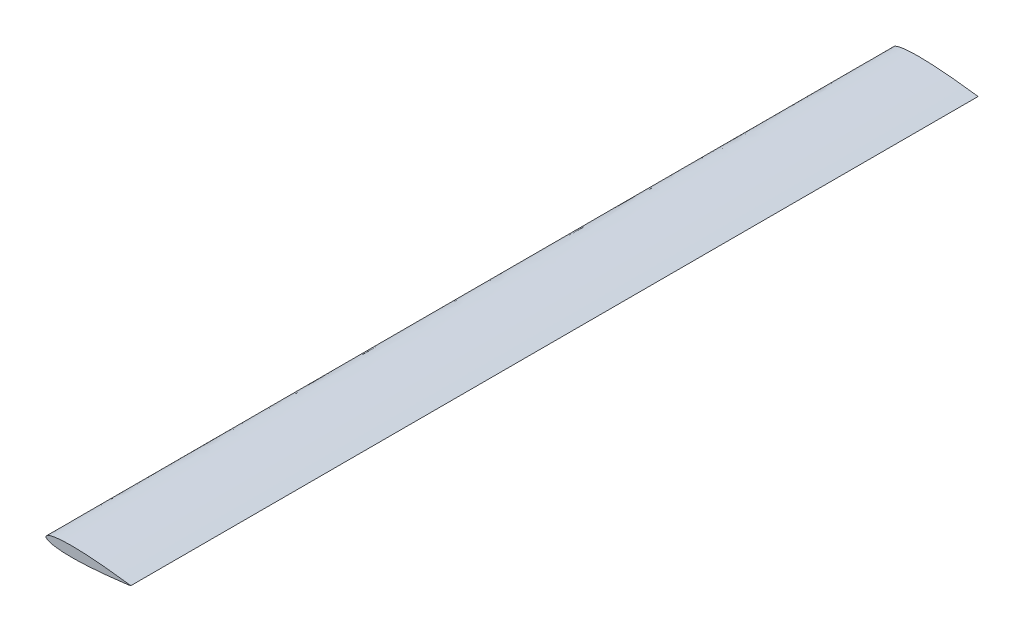
SolidWorks part; units mm, degrees
material "Custom Polymer"
ref_plane "Front Plane" through (0, 0, 0) normal (0, 0, 1) x (1, 0, 0)
ref_plane "Top Plane" through (0, 0, 0) normal (0, 1, 0) x (1, 0, 0)
ref_plane "Right Plane" through (0, 0, 0) normal (1, 0, 0) x (0, 0, -1)
other "Center of Mass"
sketch "Sketch1" plane through (0, 0, 0) normal (0, 0, 1) x (1, 0, 0)
  line L0 (0, 0) -> (1000, 0) construction
  spline S4 degree 3 poles (0.4143, 4.3853) (-0.2008, 0.0001) (0.4094, -4.3857) (2.2543, -8.6603) (5.2707, -12.775) (9.422, -16.7475) (14.6946, -20.592) (21.081, -24.312) (28.5717, -27.9033) (37.1535, -31.3578) (46.8093, -34.6651) (57.5186, -37.8143) (69.2578, -40.7934) (82.0003, -43.5917) (95.717, -46.1976) (110.3762, -48.6018) (125.9441, -50.7943) (142.3846, -52.7677) (159.6593, -54.5151) (177.7281, -56.0316) (196.5487, -57.3135) (216.0775, -58.3589) (236.2687, -59.1679) (257.0752, -59.7419) (278.4485, -60.0841) (300.3387, -60.1994) (322.6946, -60.0941) (345.4641, -59.7758) (368.5941, -59.2535) (392.0304, -58.5372) (415.7184, -57.6376) (439.6028, -56.5665) (463.6278, -55.336) (487.7372, -53.9588) (511.8749, -52.4476) (535.9844, -50.8155) (560.0094, -49.0752) (583.8939, -47.2399) (607.5819, -45.322) (631.0183, -43.3341) (654.1483, -41.2882) (676.9179, -39.1961) (699.2738, -37.0696) (721.1639, -34.9196) (742.5371, -32.7573) (763.3433, -30.5932) (783.5341, -28.438) (803.0622, -26.3022) (821.8821, -24.1954) (839.9497, -22.1283) (857.223, -20.1106) (873.6615, -18.1522) (889.2267, -16.2628) (903.8825, -14.4523) (917.5946, -12.7298) (930.3308, -11.1051) (942.0615, -9.5864) (952.7594, -8.1834) (962.3991, -6.9024) (970.9591, -5.7556) (978.4165, -4.737) (984.7625, -3.8911) (989.9579, -3.1155) (994.0559, -2.7031) (996.8878, -1.9572) (999.5116, -2.4521) (1000.4888, 0.7707) (998.6373, 0.7843) (996.9769, 1.1296) (994.0179, 1.481) (989.9767, 2.0732) (984.7604, 2.7864) (978.4232, 3.6639) (970.9642, 4.6823) (962.4063, 5.8413) (952.7678, 7.1321) (942.0716, 8.5471) (930.3425, 10.0787) (917.6081, 11.7175) (903.8979, 13.4551) (889.2441, 15.2818) (873.6809, 17.1884) (857.2446, 19.1649) (839.9736, 21.2016) (821.9083, 23.2886) (803.0908, 25.4162) (783.565, 27.5735) (763.3766, 29.751) (742.5728, 31.9381) (721.202, 34.124) (699.3143, 36.2981) (676.9607, 38.4492) (654.1935, 40.5664) (631.0658, 42.6379) (607.6316, 44.6517) (583.9456, 46.5957) (560.0632, 48.4573) (536.0401, 50.2241) (511.9324, 51.8829) (487.7965, 53.4207) (463.6885, 54.8245) (439.6649, 56.0815) (415.7818, 57.179) (392.0947, 58.1047) (368.6592, 58.8468) (345.5299, 59.3946) (322.7607, 59.7381) (300.4049, 59.868) (278.5146, 59.7768) (257.1409, 59.4583) (236.3338, 58.9072) (216.1417, 58.1205) (196.6118, 57.0967) (177.7898, 55.8354) (159.7194, 54.3389) (142.4427, 52.6106) (126.0001, 50.6553) (110.4297, 48.48) (95.7679, 46.092) (82.0483, 43.5012) (69.3028, 40.717) (57.5603, 37.7508) (46.8475, 34.6134) (37.188, 31.3167) (28.6024, 27.8718) (21.1078, 24.2887) (14.7173, 20.5758) (9.4405, 16.7371) (5.2848, 12.7691) (2.2639, 8.6578) (0.4143, 4.3853) (-0.2008, 0.0001) (0.4094, -4.3857) knots -0.006774 -0.004322 -0.002107 0 0.002107 0.004322 0.006774 0.009559 0.012737 0.016346 0.02041 0.02494 0.02994 0.03541 0.041346 0.047742 0.054587 0.061871 0.06958 0.077699 0.086213 0.095105 0.104356 0.113946 0.123856 0.134064 0.144547 0.155282 0.166246 0.177414 0.188761 0.20026 0.211886 0.223612 0.23541 0.247253 0.259115 0.270966 0.28278 0.294528 0.306184 0.31772 0.329108 0.340322 0.351336 0.362124 0.37266 0.382919 0.392878 0.402513 0.4118 0.42072 0.429249 0.437368 0.445058 0.452301 0.459079 0.465376 0.471177 0.476469 0.481238 0.485474 0.489166 0.492305 0.494884 0.496896 0.498337 0.499202 0.500509 0.500798 0.501663 0.503104 0.505116 0.507695 0.510834 0.514526 0.518762 0.523531 0.528823 0.534624 0.540921 0.547699 0.554942 0.562632 0.570751 0.57928 0.5882 0.597487 0.607122 0.617081 0.62734 0.637876 0.648664 0.659678 0.670892 0.68228 0.693816 0.705472 0.71722 0.729034 0.740885 0.752747 0.76459 0.776388 0.788114 0.79974 0.811239 0.822586 0.833754 0.844718 0.855453 0.865936 0.876144 0.886054 0.895644 0.904895 0.913787 0.922301 0.93042 0.938129 0.945413 0.952258 0.958654 0.96459 0.97006 0.97506 0.97959 0.983654 0.987263 0.990441 0.993226 0.995678 0.997893 1 1.002107 1.004322 1.006774 only from (0, 0) to (0, 0)
  dimension "D1" = 1000
extrude "Boss-Extrude1" add sketch "Sketch1" along normal blind 10000
sketch "Sketch3" plane through (0, 0, 0) normal (0, 0, -1) x (-1, 0, 0)
  line L0 (-46.6725, -5.2388) -> (-46.6725, 5.2387) construction
  line L1 (-27.6225, 5.2388) -> (-27.6225, -5.2388) construction
  line L2 (-7.7788, -3.8184) -> (-7.7788, 3.8184) construction
  line L3 (-71.2788, 3.6758) -> (-71.2788, -3.6758) construction
  line L4 (-46.6725, -5.2388) -> (-46.6725, 5.2387)
  line L5 (-27.6225, 5.2388) -> (-27.6225, -5.2388)
  line L6 (-7.7788, -3.8184) -> (-7.7788, 3.8184)
  line L7 (-71.2788, 3.6758) -> (-71.2788, -3.6758)
  arc A0 (-71.2788, -3.6758) -> (-46.6725, -5.2388) centre (-26.6642, 504.2394) ccw construction
  arc A1 (-46.6725, 5.2387) -> (-71.2788, 3.6758) centre (-26.6642, -504.2394) ccw construction
  circle A2 centre (-35.56, 0) radius 3.1433 construction
  circle A3 centre (-3.0163, 0) radius 2.9766 construction
  arc A4 (-71.2788, -3.6758) -> (-46.6725, -5.2388) centre (-26.6642, 504.2394) ccw
  arc A5 (-46.6725, 5.2387) -> (-71.2788, 3.6758) centre (-26.6642, -504.2394) ccw
  circle A6 centre (-35.56, 0) radius 3.1433
  circle A7 centre (-3.0163, 0) radius 2.9766
  circle A8 centre (-21.2725, 0) radius 3.9688
  circle A9 centre (-53.0225, 0) radius 3.9687
  spline S0 degree 3 poles (8.8377, -0.5571) (8.9155, 0) (8.8377, 0.5571) (8.603, 1.1001) (8.2195, 1.6226) (7.6918, 2.127) (7.0217, 2.615) (6.2101, 3.0872) (5.2582, 3.5429) (4.1677, 3.9812) (2.9408, 4.4007) (1.58, 4.8) (0.0884, 5.1777) (-1.5306, 5.5323) (-3.2734, 5.8624) (-5.1359, 6.1668) (-7.1139, 6.4442) (-9.2026, 6.6938) (-11.3974, 6.9146) (-13.693, 7.106) (-16.0841, 7.2675) (-18.5652, 7.3989) (-21.1304, 7.5003) (-23.7737, 7.5718) (-26.4891, 7.6137) (-29.2701, 7.6269) (-32.1103, 7.6119) (-35.0029, 7.5699) (-37.9414, 7.5019) (-40.9188, 7.4093) (-43.9281, 7.2933) (-46.9624, 7.1556) (-50.0145, 6.9976) (-53.0773, 6.8209) (-56.1437, 6.6272) (-59.2065, 6.4182) (-62.2586, 6.1954) (-65.2928, 5.9606) (-68.3021, 5.7153) (-71.2794, 5.4611) (-74.2178, 5.1995) (-77.1103, 4.9321) (-79.9503, 4.6604) (-82.7312, 4.3857) (-85.4463, 4.1095) (-88.0894, 3.8332) (-90.6544, 3.5579) (-93.1352, 3.2852) (-95.5259, 3.0163) (-97.8211, 2.7524) (-100.0154, 2.4948) (-102.1037, 2.2449) (-104.081, 2.0038) (-105.9428, 1.7727) (-107.6847, 1.5529) (-109.3027, 1.3456) (-110.7928, 1.1519) (-112.1518, 0.9728) (-113.3764, 0.8095) (-114.4637, 0.6629) (-115.4114, 0.534) (-116.2166, 0.423) (-116.8793, 0.3328) (-117.3928, 0.2578) (-117.7687, 0.2134) (-117.9797, 0.1696) (-118.2149, 0.168) (-118.091, -0.2415) (-117.7576, -0.1788) (-117.3979, -0.2737) (-116.8773, -0.3264) (-116.2173, -0.4253) (-115.4111, -0.5332) (-114.4638, -0.6632) (-113.3764, -0.8095) (-112.1518, -0.9729) (-110.7928, -1.1519) (-109.3027, -1.3456) (-107.6847, -1.5529) (-105.9428, -1.7727) (-104.081, -2.0038) (-102.1037, -2.2449) (-100.0154, -2.4948) (-97.8211, -2.7524) (-95.5259, -3.0163) (-93.1352, -3.2852) (-90.6544, -3.5579) (-88.0894, -3.8332) (-85.4463, -4.1095) (-82.7312, -4.3857) (-79.9503, -4.6604) (-77.1103, -4.9321) (-74.2178, -5.1995) (-71.2794, -5.4611) (-68.3021, -5.7153) (-65.2928, -5.9606) (-62.2586, -6.1954) (-59.2065, -6.4182) (-56.1437, -6.6272) (-53.0773, -6.8209) (-50.0145, -6.9976) (-46.9624, -7.1556) (-43.9281, -7.2933) (-40.9188, -7.4093) (-37.9414, -7.5019) (-35.0029, -7.5699) (-32.1103, -7.6119) (-29.2701, -7.6269) (-26.4891, -7.6137) (-23.7737, -7.5718) (-21.1304, -7.5003) (-18.5652, -7.3989) (-16.0841, -7.2675) (-13.693, -7.106) (-11.3974, -6.9146) (-9.2026, -6.6938) (-7.1139, -6.4442) (-5.1359, -6.1668) (-3.2734, -5.8624) (-1.5306, -5.5323) (0.0884, -5.1777) (1.58, -4.8) (2.9408, -4.4007) (4.1677, -3.9812) (5.2582, -3.5429) (6.2101, -3.0872) (7.0217, -2.615) (7.6918, -2.127) (8.2195, -1.6226) (8.603, -1.1001) (8.8377, -0.5571) (8.9155, 0) (8.8377, 0.5571) knots -0.006774 -0.004322 -0.002107 0 0.002107 0.004322 0.006774 0.009559 0.012737 0.016346 0.02041 0.02494 0.02994 0.03541 0.041346 0.047742 0.054587 0.061871 0.06958 0.077699 0.086213 0.095105 0.104356 0.113946 0.123856 0.134064 0.144547 0.155282 0.166246 0.177414 0.188761 0.20026 0.211886 0.223612 0.23541 0.247253 0.259115 0.270966 0.28278 0.294528 0.306184 0.31772 0.329108 0.340322 0.351336 0.362124 0.37266 0.382919 0.392878 0.402513 0.4118 0.42072 0.429249 0.437368 0.445058 0.452301 0.459079 0.465376 0.471177 0.476469 0.481238 0.485474 0.489166 0.492305 0.494884 0.496896 0.498337 0.499202 0.499491 0.500798 0.501663 0.503104 0.505116 0.507695 0.510834 0.514526 0.518762 0.523531 0.528823 0.534624 0.540921 0.547699 0.554942 0.562632 0.570751 0.57928 0.5882 0.597487 0.607122 0.617081 0.62734 0.637876 0.648664 0.659678 0.670892 0.68228 0.693816 0.705472 0.71722 0.729034 0.740885 0.752747 0.76459 0.776388 0.788114 0.79974 0.811239 0.822586 0.833754 0.844718 0.855453 0.865936 0.876144 0.886054 0.895644 0.904895 0.913787 0.922301 0.93042 0.938129 0.945413 0.952258 0.958654 0.96459 0.97006 0.97506 0.97959 0.983654 0.987263 0.990441 0.993226 0.995678 0.997893 1 1.002107 1.004322 1.006774 only from (8.89, 0) to (8.89, 0) construction
  spline S1 degree 3 poles (-27.6225, 5.2388) (-20.0778, 5.0313) (-13.2778, 4.5445) (-7.7788, 3.8184) knots 0 0 0 0 1 1 1 1 weights 1 0.972728 0.972728 1 construction
  spline S2 degree 3 poles (-27.6225, -5.2388) (-20.0778, -5.0313) (-13.2778, -4.5445) (-7.7788, -3.8184) knots 0 0 0 0 1 1 1 1 weights 1 0.972728 0.972728 1 construction
  spline S3 degree 3 poles (8.8377, -0.5571) (8.9155, 0) (8.8377, 0.5571) (8.603, 1.1001) (8.2195, 1.6226) (7.6918, 2.127) (7.0217, 2.615) (6.2101, 3.0872) (5.2582, 3.5429) (4.1677, 3.9812) (2.9408, 4.4007) (1.58, 4.8) (0.0884, 5.1777) (-1.5306, 5.5323) (-3.2734, 5.8624) (-5.1359, 6.1668) (-7.1139, 6.4442) (-9.2026, 6.6938) (-11.3974, 6.9146) (-13.693, 7.106) (-16.0841, 7.2675) (-18.5652, 7.3989) (-21.1304, 7.5003) (-23.7737, 7.5718) (-26.4891, 7.6137) (-29.2701, 7.6269) (-32.1103, 7.6119) (-35.0029, 7.5699) (-37.9414, 7.5019) (-40.9188, 7.4093) (-43.9281, 7.2933) (-46.9624, 7.1556) (-50.0145, 6.9976) (-53.0773, 6.8209) (-56.1437, 6.6272) (-59.2065, 6.4182) (-62.2586, 6.1954) (-65.2928, 5.9606) (-68.3021, 5.7153) (-71.2794, 5.4611) (-74.2178, 5.1995) (-77.1103, 4.9321) (-79.9503, 4.6604) (-82.7312, 4.3857) (-85.4463, 4.1095) (-88.0894, 3.8332) (-90.6544, 3.5579) (-93.1352, 3.2852) (-95.5259, 3.0163) (-97.8211, 2.7524) (-100.0154, 2.4948) (-102.1037, 2.2449) (-104.081, 2.0038) (-105.9428, 1.7727) (-107.6847, 1.5529) (-109.3027, 1.3456) (-110.7928, 1.1519) (-112.1518, 0.9728) (-113.3764, 0.8095) (-114.4637, 0.6629) (-115.4114, 0.534) (-116.2166, 0.423) (-116.8793, 0.3328) (-117.3928, 0.2578) (-117.7687, 0.2134) (-117.9797, 0.1696) (-118.2149, 0.168) (-118.091, -0.2415) (-117.7576, -0.1788) (-117.3979, -0.2737) (-116.8773, -0.3264) (-116.2173, -0.4253) (-115.4111, -0.5332) (-114.4638, -0.6632) (-113.3764, -0.8095) (-112.1518, -0.9729) (-110.7928, -1.1519) (-109.3027, -1.3456) (-107.6847, -1.5529) (-105.9428, -1.7727) (-104.081, -2.0038) (-102.1037, -2.2449) (-100.0154, -2.4948) (-97.8211, -2.7524) (-95.5259, -3.0163) (-93.1352, -3.2852) (-90.6544, -3.5579) (-88.0894, -3.8332) (-85.4463, -4.1095) (-82.7312, -4.3857) (-79.9503, -4.6604) (-77.1103, -4.9321) (-74.2178, -5.1995) (-71.2794, -5.4611) (-68.3021, -5.7153) (-65.2928, -5.9606) (-62.2586, -6.1954) (-59.2065, -6.4182) (-56.1437, -6.6272) (-53.0773, -6.8209) (-50.0145, -6.9976) (-46.9624, -7.1556) (-43.9281, -7.2933) (-40.9188, -7.4093) (-37.9414, -7.5019) (-35.0029, -7.5699) (-32.1103, -7.6119) (-29.2701, -7.6269) (-26.4891, -7.6137) (-23.7737, -7.5718) (-21.1304, -7.5003) (-18.5652, -7.3989) (-16.0841, -7.2675) (-13.693, -7.106) (-11.3974, -6.9146) (-9.2026, -6.6938) (-7.1139, -6.4442) (-5.1359, -6.1668) (-3.2734, -5.8624) (-1.5306, -5.5323) (0.0884, -5.1777) (1.58, -4.8) (2.9408, -4.4007) (4.1677, -3.9812) (5.2582, -3.5429) (6.2101, -3.0872) (7.0217, -2.615) (7.6918, -2.127) (8.2195, -1.6226) (8.603, -1.1001) (8.8377, -0.5571) (8.9155, 0) (8.8377, 0.5571) knots -0.006774 -0.004322 -0.002107 0 0.002107 0.004322 0.006774 0.009559 0.012737 0.016346 0.02041 0.02494 0.02994 0.03541 0.041346 0.047742 0.054587 0.061871 0.06958 0.077699 0.086213 0.095105 0.104356 0.113946 0.123856 0.134064 0.144547 0.155282 0.166246 0.177414 0.188761 0.20026 0.211886 0.223612 0.23541 0.247253 0.259115 0.270966 0.28278 0.294528 0.306184 0.31772 0.329108 0.340322 0.351336 0.362124 0.37266 0.382919 0.392878 0.402513 0.4118 0.42072 0.429249 0.437368 0.445058 0.452301 0.459079 0.465376 0.471177 0.476469 0.481238 0.485474 0.489166 0.492305 0.494884 0.496896 0.498337 0.499202 0.499491 0.500798 0.501663 0.503104 0.505116 0.507695 0.510834 0.514526 0.518762 0.523531 0.528823 0.534624 0.540921 0.547699 0.554942 0.562632 0.570751 0.57928 0.5882 0.597487 0.607122 0.617081 0.62734 0.637876 0.648664 0.659678 0.670892 0.68228 0.693816 0.705472 0.71722 0.729034 0.740885 0.752747 0.76459 0.776388 0.788114 0.79974 0.811239 0.822586 0.833754 0.844718 0.855453 0.865936 0.876144 0.886054 0.895644 0.904895 0.913787 0.922301 0.93042 0.938129 0.945413 0.952258 0.958654 0.96459 0.97006 0.97506 0.97959 0.983654 0.987263 0.990441 0.993226 0.995678 0.997893 1 1.002107 1.004322 1.006774 only from (8.89, 0) to (8.89, 0)
  spline S4 degree 3 poles (-27.6225, 5.2388) (-20.0778, 5.0313) (-13.2778, 4.5445) (-7.7788, 3.8184) knots 0 0 0 0 1 1 1 1 weights 1 0.972728 0.972728 1
  spline S5 degree 3 poles (-27.6225, -5.2388) (-20.0778, -5.0313) (-13.2778, -4.5445) (-7.7788, -3.8184) knots 0 0 0 0 1 1 1 1 weights 1 0.972728 0.972728 1
  dimension "D2" = 7.9375
  dimension "D3" = 7.9375
  dimension "D1" = 6.35
  dimension "D4" = 6.35
extrude "Boss-Extrude2" [suppressed] add sketch "Sketch3" along normal blind 6.35
pattern_linear "LPattern1" [suppressed] count 3 spacing 69.85
sketch "Sketch5" [suppressed] plane through (0, 0, -139.7) normal (0, 0, 1) x (1, 0, 0)
  line L2 (71.2787, -3.6758) -> (71.2788, 3.6758)
  line L3 (46.6725, 5.2387) -> (46.6725, -5.2388)
  line L4 (71.2787, -3.6758) -> (71.2788, 3.6758)
  line L5 (46.6725, 5.2387) -> (46.6725, -5.2388)
  arc A2 (46.6725, -5.2388) -> (71.2787, -3.6758) centre (26.6642, 504.2394) ccw
  arc A3 (71.2788, 3.6758) -> (46.6725, 5.2387) centre (26.6642, -504.2394) ccw
  arc A4 (46.6725, -5.2388) -> (71.2787, -3.6758) centre (26.6642, 504.2394) ccw
  arc A5 (71.2788, 3.6758) -> (46.6725, 5.2387) centre (26.6642, -504.2394) ccw
  dimension "D1" = 0
extrude "Cut-Extrude1" [suppressed] cut sketch "Sketch5" against normal blind 6.35
sketch "Sketch6" [suppressed] plane through (0, 0, -139.7) normal (0, 0, 1) x (1, 0, 0)
  line L2 (27.6225, -5.2388) -> (27.6225, 5.2388)
  line L3 (7.7788, 3.8184) -> (7.7788, -3.8184)
  line L4 (27.6225, -5.2388) -> (27.6225, 5.2388)
  line L5 (7.7788, 3.8184) -> (7.7788, -3.8184)
  spline S2 degree 3 poles (7.7788, -3.8184) (13.2778, -4.5445) (20.0778, -5.0313) (27.6225, -5.2388) knots 0 0 0 0 1 1 1 1 weights 1 0.972728 0.972728 1
  spline S3 degree 3 poles (27.6225, 5.2388) (20.0778, 5.0313) (13.2778, 4.5445) (7.7788, 3.8184) knots 0 0 0 0 1 1 1 1 weights 1 0.972728 0.972728 1
  spline S4 degree 3 poles (7.7788, -3.8184) (13.2778, -4.5445) (20.0778, -5.0313) (27.6225, -5.2388) knots 0 0 0 0 1 1 1 1 weights 1 0.972728 0.972728 1
  spline S5 degree 3 poles (27.6225, 5.2388) (20.0778, 5.0313) (13.2778, 4.5445) (7.7788, 3.8184) knots 0 0 0 0 1 1 1 1 weights 1 0.972728 0.972728 1
  dimension "D1" = 0
extrude "Cut-Extrude2" [suppressed] cut sketch "Sketch6" against normal blind 6.35
sketch "Sketch8" [suppressed] plane through (0, 0, 609.6) normal (0, 0, 1) x (1, 0, 0)
  line L0 (35.56, 0) -> (-8.89, 0) construction
  spline S0 degree 3 poles (-8.8377, 0.5571) (-8.9155, 0) (-8.8377, -0.5571) (-8.603, -1.1001) (-8.2195, -1.6226) (-7.6918, -2.127) (-7.0217, -2.615) (-6.2101, -3.0872) (-5.2582, -3.5429) (-4.1677, -3.9812) (-2.9408, -4.4007) (-1.58, -4.8) (-0.0884, -5.1777) (1.5306, -5.5323) (3.2734, -5.8624) (5.1359, -6.1668) (7.1139, -6.4442) (9.2026, -6.6938) (11.3974, -6.9146) (13.693, -7.106) (16.0841, -7.2675) (18.5652, -7.3989) (21.1304, -7.5003) (23.7737, -7.5718) (26.4891, -7.6137) (29.2701, -7.6269) (32.1103, -7.6119) (35.0029, -7.5699) (37.9414, -7.5019) (40.9188, -7.4093) (43.9281, -7.2933) (46.9624, -7.1556) (50.0145, -6.9976) (53.0773, -6.8209) (56.1437, -6.6272) (59.2065, -6.4182) (62.2586, -6.1954) (65.2928, -5.9606) (68.3021, -5.7153) (71.2794, -5.4611) (74.2178, -5.1995) (77.1103, -4.9321) (79.9503, -4.6604) (82.7312, -4.3857) (85.4463, -4.1095) (88.0894, -3.8332) (90.6544, -3.5579) (93.1352, -3.2852) (95.5259, -3.0163) (97.8211, -2.7524) (100.0154, -2.4948) (102.1037, -2.2449) (104.081, -2.0038) (105.9428, -1.7727) (107.6847, -1.5529) (109.3027, -1.3456) (110.7928, -1.1519) (112.1518, -0.9729) (113.3764, -0.8095) (114.4638, -0.6632) (115.4111, -0.5332) (116.2173, -0.4253) (116.8773, -0.3264) (117.3979, -0.2737) (117.7576, -0.1788) (118.091, -0.2415) (118.2149, 0.168) (117.9797, 0.1696) (117.7687, 0.2134) (117.3928, 0.2578) (116.8793, 0.3328) (116.2166, 0.423) (115.4114, 0.534) (114.4637, 0.6629) (113.3764, 0.8095) (112.1518, 0.9728) (110.7928, 1.1519) (109.3027, 1.3456) (107.6847, 1.5529) (105.9428, 1.7727) (104.081, 2.0038) (102.1037, 2.2449) (100.0154, 2.4948) (97.8211, 2.7524) (95.5259, 3.0163) (93.1352, 3.2852) (90.6544, 3.5579) (88.0894, 3.8332) (85.4463, 4.1095) (82.7312, 4.3857) (79.9503, 4.6604) (77.1103, 4.9321) (74.2178, 5.1995) (71.2794, 5.4611) (68.3021, 5.7153) (65.2928, 5.9606) (62.2586, 6.1954) (59.2065, 6.4182) (56.1437, 6.6272) (53.0773, 6.8209) (50.0145, 6.9976) (46.9624, 7.1556) (43.9281, 7.2933) (40.9188, 7.4093) (37.9414, 7.5019) (35.0029, 7.5699) (32.1103, 7.6119) (29.2701, 7.6269) (26.4891, 7.6137) (23.7737, 7.5718) (21.1304, 7.5003) (18.5652, 7.3989) (16.0841, 7.2675) (13.693, 7.106) (11.3974, 6.9146) (9.2026, 6.6938) (7.1139, 6.4442) (5.1359, 6.1668) (3.2734, 5.8624) (1.5306, 5.5323) (-0.0884, 5.1777) (-1.58, 4.8) (-2.9408, 4.4007) (-4.1677, 3.9812) (-5.2582, 3.5429) (-6.2101, 3.0872) (-7.0217, 2.615) (-7.6918, 2.127) (-8.2195, 1.6226) (-8.603, 1.1001) (-8.8377, 0.5571) (-8.9155, 0) (-8.8377, -0.5571) knots -0.006774 -0.004322 -0.002107 0 0.002107 0.004322 0.006774 0.009559 0.012737 0.016346 0.02041 0.02494 0.02994 0.03541 0.041346 0.047742 0.054587 0.061871 0.06958 0.077699 0.086213 0.095105 0.104356 0.113946 0.123856 0.134064 0.144547 0.155282 0.166246 0.177414 0.188761 0.20026 0.211886 0.223612 0.23541 0.247253 0.259115 0.270966 0.28278 0.294528 0.306184 0.31772 0.329108 0.340322 0.351336 0.362124 0.37266 0.382919 0.392878 0.402513 0.4118 0.42072 0.429249 0.437368 0.445058 0.452301 0.459079 0.465376 0.471177 0.476469 0.481238 0.485474 0.489166 0.492305 0.494884 0.496896 0.498337 0.499202 0.500509 0.500798 0.501663 0.503104 0.505116 0.507695 0.510834 0.514526 0.518762 0.523531 0.528823 0.534624 0.540921 0.547699 0.554942 0.562632 0.570751 0.57928 0.5882 0.597487 0.607122 0.617081 0.62734 0.637876 0.648664 0.659678 0.670892 0.68228 0.693816 0.705472 0.71722 0.729034 0.740885 0.752747 0.76459 0.776388 0.788114 0.79974 0.811239 0.822586 0.833754 0.844718 0.855453 0.865936 0.876144 0.886054 0.895644 0.904895 0.913787 0.922301 0.93042 0.938129 0.945413 0.952258 0.958654 0.96459 0.97006 0.97506 0.97959 0.983654 0.987263 0.990441 0.993226 0.995678 0.997893 1 1.002107 1.004322 1.006774 only from (-8.89, 0) to (-8.89, 0) construction
